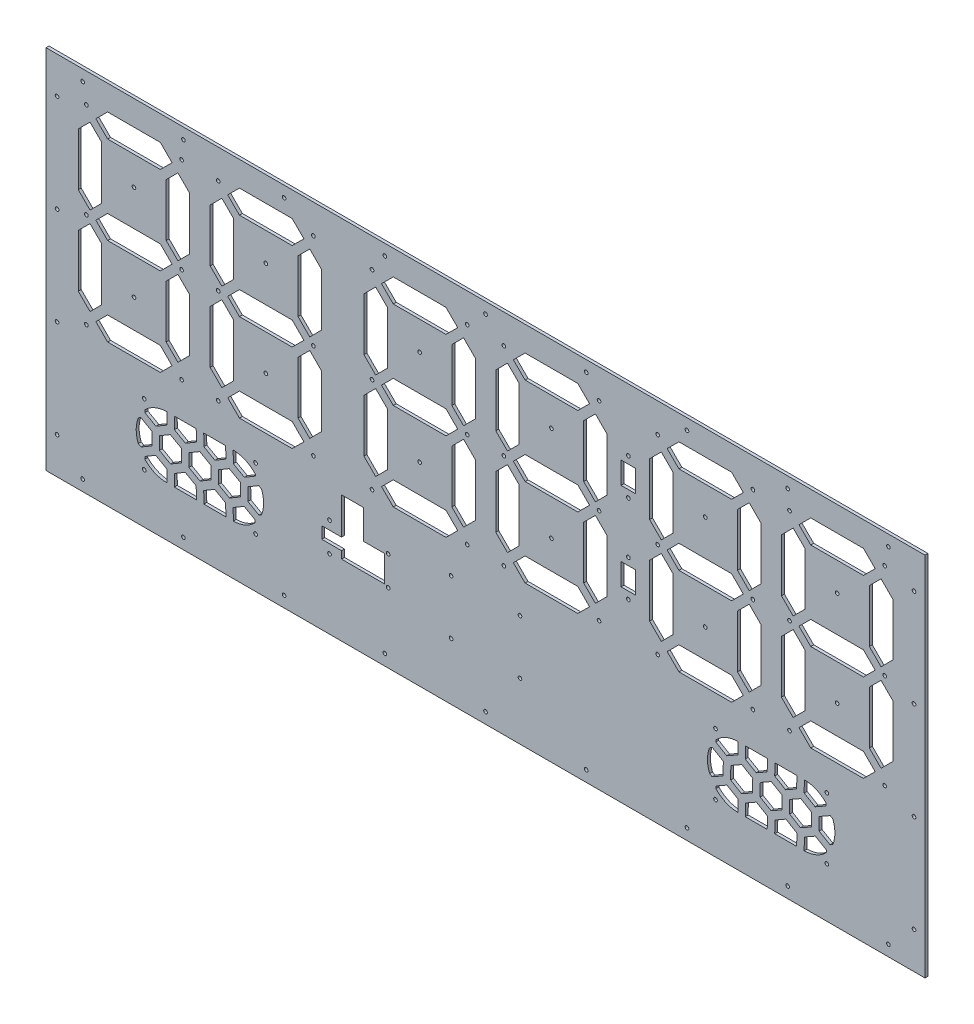
SolidWorks part; units mm, degrees
ref_plane "Alzado" through (0, 0, 0) normal (0, 0, 1) x (1, 0, 0)
ref_plane "Planta" through (0, 0, 0) normal (0, 1, 0) x (1, 0, 0)
ref_plane "Vista lateral" through (0, 0, 0) normal (1, 0, 0) x (0, 0, -1)
sketch "Croquis2" plane through (0, 0, 0) normal (0, 0, 1) x (1, 0, 0)
  line L1 (-300, -125) -> (300, -125)
  line L2 (-300, -125) -> (-300, 125)
  line L3 (-300, 125) -> (300, 125)
  line L4 (300, -125) -> (300, 125)
  line L5 (-300, -125) -> (300, 125) construction
  line L6 (-300, 125) -> (300, -125) construction
  point P0 (0, 0)
extrude "Saliente-Extruir1" add sketch "Croquis2" along normal blind 4
sketch "Croquis4" plane through (0, 0, 0) normal (0, 0, -1) x (-1, 0, 0)
  line L0 (0, 125) -> (0, 40) construction
  line L2 (-300, 125) -> (300, 125) construction
  line B0 (222, 92) -> (214, 100)
  line B1 (214, 100) -> (222, 108)
  line B2 (222, 108) -> (258, 108)
  line B3 (258, 108) -> (266, 100)
  line B4 (266, 100) -> (258, 92)
  line B5 (258, 92) -> (222, 92)
  line B6 (-262, -8) -> (-270, -16)
  line B7 (-270, -16) -> (-278, -8)
  line B8 (-278, -8) -> (-278, 28)
  line B9 (-278, 28) -> (-270, 36)
  line B10 (-270, 36) -> (-262, 28)
  line B11 (-262, 28) -> (-262, -8)
  line B12 (-222, 100) -> (-258, 100) construction
  line B13 (-258, 92) -> (-266, 100)
  line B14 (-266, 100) -> (-258, 108)
  line B15 (-258, 108) -> (-222, 108)
  line B16 (-222, 108) -> (-214, 100)
  line B17 (-214, 100) -> (-222, 92)
  line B18 (-222, 92) -> (-258, 92)
  line B19 (-168, -12) -> (-176, -20)
  line B20 (-176, -20) -> (-168, -28)
  line B21 (-168, -28) -> (-132, -28)
  line B22 (-132, -28) -> (-124, -20)
  line B23 (-124, -20) -> (-132, -12)
  line B24 (-132, -12) -> (-168, -12)
  line B25 (222, 32) -> (214, 40)
  line B26 (214, 40) -> (222, 48)
  line B27 (222, 48) -> (258, 48)
  line B28 (258, 48) -> (266, 40)
  line B29 (266, 40) -> (258, 32)
  line B30 (258, 32) -> (222, 32)
  line B31 (-168, 92) -> (-176, 100)
  line B32 (-176, 100) -> (-168, 108)
  line B33 (-168, 108) -> (-132, 108)
  line B34 (-132, 108) -> (-124, 100)
  line B35 (-124, 100) -> (-132, 92)
  line B36 (-132, 92) -> (-168, 92)
  line B37 (222, -12) -> (214, -20)
  line B38 (214, -20) -> (222, -28)
  line B39 (222, -28) -> (258, -28)
  line B40 (258, -28) -> (266, -20)
  line B41 (266, -20) -> (258, -12)
  line B42 (258, -12) -> (222, -12)
  line B43 (262, -8) -> (270, -16)
  line B44 (270, -16) -> (278, -8)
  line B45 (278, -8) -> (278, 28)
  line B46 (278, 28) -> (270, 36)
  line B47 (270, 36) -> (262, 28)
  line B48 (262, 28) -> (262, -8)
  line B49 (218, 88) -> (210, 96)
  line B50 (210, 96) -> (202, 88)
  line B51 (202, 88) -> (202, 52)
  line B52 (202, 52) -> (210, 44)
  line B53 (210, 44) -> (218, 52)
  line B54 (218, 52) -> (218, 88)
  line B55 (218, -8) -> (210, -16)
  line B56 (210, -16) -> (202, -8)
  line B57 (202, -8) -> (202, 28)
  line B58 (202, 28) -> (210, 36)
  line B59 (210, 36) -> (218, 28)
  line B60 (218, 28) -> (218, -8)
  line B61 (-128, -8) -> (-120, -16)
  line B62 (-120, -16) -> (-112, -8)
  line B63 (-112, -8) -> (-112, 28)
  line B64 (-112, 28) -> (-120, 36)
  line B65 (-120, 36) -> (-128, 28)
  line B66 (-128, 28) -> (-128, -8)
  line B67 (-168, 32) -> (-176, 40)
  line B68 (-176, 40) -> (-168, 48)
  line B69 (-168, 48) -> (-132, 48)
  line B70 (-132, 48) -> (-124, 40)
  line B71 (-124, 40) -> (-132, 32)
  line B72 (-132, 32) -> (-168, 32)
  line B73 (-262, 88) -> (-270, 96)
  line B74 (-270, 96) -> (-278, 88)
  line B75 (-278, 88) -> (-278, 52)
  line B76 (-278, 52) -> (-270, 44)
  line B77 (-270, 44) -> (-262, 52)
  line B78 (-262, 52) -> (-262, 88)
  line B79 (262, 88) -> (270, 96)
  line B80 (270, 96) -> (278, 88)
  line B81 (278, 88) -> (278, 52)
  line B82 (278, 52) -> (270, 44)
  line B83 (270, 44) -> (262, 52)
  line B84 (262, 52) -> (262, 88)
  line B85 (-218, 88) -> (-210, 96)
  line B86 (-210, 96) -> (-202, 88)
  line B87 (-202, 88) -> (-202, 52)
  line B88 (-202, 52) -> (-210, 44)
  line B89 (-210, 44) -> (-218, 52)
  line B90 (-218, 52) -> (-218, 88)
  line B91 (-258, 32) -> (-266, 40)
  line B92 (-266, 40) -> (-258, 48)
  line B93 (-258, 48) -> (-222, 48)
  line B94 (-222, 48) -> (-214, 40)
  line B95 (-214, 40) -> (-222, 32)
  line B96 (-222, 32) -> (-258, 32)
  line B97 (-218, -8) -> (-210, -16)
  line B98 (-210, -16) -> (-202, -8)
  line B99 (-202, -8) -> (-202, 28)
  line B100 (-202, 28) -> (-210, 36)
  line B101 (-210, 36) -> (-218, 28)
  line B102 (-218, 28) -> (-218, -8)
  line B103 (-258, -12) -> (-266, -20)
  line B104 (-266, -20) -> (-258, -28)
  line B105 (-258, -28) -> (-222, -28)
  line B106 (-222, -28) -> (-214, -20)
  line B107 (-214, -20) -> (-222, -12)
  line B108 (-222, -12) -> (-258, -12)
  line B109 (128, 88) -> (120, 96)
  line B110 (120, 96) -> (112, 88)
  line B111 (112, 88) -> (112, 52)
  line B112 (112, 52) -> (120, 44)
  line B113 (120, 44) -> (128, 52)
  line B114 (128, 52) -> (128, 88)
  line B115 (132, 92) -> (124, 100)
  line B116 (124, 100) -> (132, 108)
  line B117 (132, 108) -> (168, 108)
  line B118 (168, 108) -> (176, 100)
  line B119 (176, 100) -> (168, 92)
  line B120 (168, 92) -> (132, 92)
  line B121 (128, -8) -> (120, -16)
  line B122 (120, -16) -> (112, -8)
  line B123 (112, -8) -> (112, 28)
  line B124 (112, 28) -> (120, 36)
  line B125 (120, 36) -> (128, 28)
  line B126 (128, 28) -> (128, -8)
  line B127 (132, -12) -> (124, -20)
  line B128 (124, -20) -> (132, -28)
  line B129 (132, -28) -> (168, -28)
  line B130 (168, -28) -> (176, -20)
  line B131 (176, -20) -> (168, -12)
  line B132 (168, -12) -> (132, -12)
  line B133 (132, 32) -> (124, 40)
  line B134 (124, 40) -> (132, 48)
  line B135 (132, 48) -> (168, 48)
  line B136 (168, 48) -> (176, 40)
  line B137 (176, 40) -> (168, 32)
  line B138 (168, 32) -> (132, 32)
  line B139 (172, -8) -> (180, -16)
  line B140 (180, -16) -> (188, -8)
  line B141 (188, -8) -> (188, 28)
  line B142 (188, 28) -> (180, 36)
  line B143 (180, 36) -> (172, 28)
  line B144 (172, 28) -> (172, -8)
  line B145 (-128, 88) -> (-120, 96)
  line B146 (-120, 96) -> (-112, 88)
  line B147 (-112, 88) -> (-112, 52)
  line B148 (-112, 52) -> (-120, 44)
  line B149 (-120, 44) -> (-128, 52)
  line B150 (-128, 52) -> (-128, 88)
  line B151 (-180, 28) -> (-180, -8) construction
  line B152 (-172, -8) -> (-180, -16)
  line B153 (-180, -16) -> (-188, -8)
  line B154 (-188, -8) -> (-188, 28)
  line B155 (-188, 28) -> (-180, 36)
  line B156 (-180, 36) -> (-172, 28)
  line B157 (-172, 28) -> (-172, -8)
  line B158 (-172, 88) -> (-180, 96)
  line B159 (-180, 96) -> (-188, 88)
  line B160 (-188, 88) -> (-188, 52)
  line B161 (-188, 52) -> (-180, 44)
  line B162 (-180, 44) -> (-172, 52)
  line B163 (-172, 52) -> (-172, 88)
  line B164 (172, 88) -> (180, 96)
  line B165 (180, 96) -> (188, 88)
  line B166 (188, 88) -> (188, 52)
  line B167 (188, 52) -> (180, 44)
  line B168 (180, 44) -> (172, 52)
  line B169 (172, 52) -> (172, 88)
  line B170 (-2.5, 40) -> (2.5, 40) construction
  line B171 (87.5, 40) -> (107.5, 40) construction
  line B172 (-87.5, 40) -> (-107.5, 40) construction
  line B173 (-87.5, 40) -> (-2.5, 40) construction
  line B174 (-45, 110) -> (-45, -30) construction
  line B175 (-45, 40) -> (-15, 40) construction
  line B176 (-15, 40) -> (-15, 44) construction
  line B177 (-75, 96) -> (-71, 96) construction
  line B178 (-71, 96) -> (-71, 100) construction
  line B179 (2.5, 40) -> (87.5, 40) construction
  line B180 (45, 110) -> (45, -30) construction
  line B181 (45, 40) -> (75, 40) construction
  line B182 (75, 40) -> (75, 44) construction
  line B183 (15, 96) -> (19, 96) construction
  line B184 (19, 96) -> (19, 100) construction
  line B185 (192.5, 40) -> (197.5, 40) construction
  line B186 (-197.5, 40) -> (-192.5, 40) construction
  line B187 (-75, 44) -> (-75, 52) construction
  line B188 (-75, 52) -> (-75, 88) construction
  line B189 (-75, 88) -> (-75, 96) construction
  line B190 (-75, 52) -> (-83, 52) construction
  line B191 (-83, 52) -> (-67, 52) construction
  line B192 (-75, 88) -> (-83, 88) construction
  line B193 (-83, 88) -> (-67, 88) construction
  line B194 (-67, 88) -> (-75, 96)
  line B195 (-75, 96) -> (-83, 88)
  line B196 (-83, 88) -> (-83, 52)
  line B197 (-83, 52) -> (-75, 44)
  line B198 (-75, 44) -> (-67, 52)
  line B199 (-67, 52) -> (-67, 88)
  line B200 (-19, -20) -> (-27, -20) construction
  line B201 (-27, -20) -> (-63, -20) construction
  line B202 (-63, -20) -> (-71, -20) construction
  line B203 (-27, -20) -> (-27, -28) construction
  line B204 (-27, -28) -> (-27, -12) construction
  line B205 (-63, -20) -> (-63, -28) construction
  line B206 (-63, -28) -> (-63, -12) construction
  line B207 (-63, -12) -> (-71, -20)
  line B208 (-71, -20) -> (-63, -28)
  line B209 (-63, -28) -> (-27, -28)
  line B210 (-27, -28) -> (-19, -20)
  line B211 (-19, -20) -> (-27, -12)
  line B212 (-27, -12) -> (-63, -12)
  line B213 (-19, 40) -> (-27, 40) construction
  line B214 (-27, 40) -> (-63, 40) construction
  line B215 (-63, 40) -> (-71, 40) construction
  line B216 (-27, 40) -> (-27, 48) construction
  line B217 (-27, 48) -> (-27, 32) construction
  line B218 (-63, 40) -> (-63, 48) construction
  line B219 (-63, 48) -> (-63, 32) construction
  line B220 (-63, 32) -> (-71, 40)
  line B221 (-71, 40) -> (-63, 48)
  line B222 (-63, 48) -> (-27, 48)
  line B223 (-27, 48) -> (-19, 40)
  line B224 (-19, 40) -> (-27, 32)
  line B225 (-27, 32) -> (-63, 32)
  line B226 (-15, 36) -> (-15, 28) construction
  line B227 (-15, 28) -> (-15, -8) construction
  line B228 (-15, -8) -> (-15, -16) construction
  line B229 (-15, 28) -> (-7, 28) construction
  line B230 (-7, 28) -> (-23, 28) construction
  line B231 (-15, -8) -> (-7, -8) construction
  line B232 (-7, -8) -> (-23, -8) construction
  line B233 (-23, -8) -> (-15, -16)
  line B234 (-15, -16) -> (-7, -8)
  line B235 (-7, -8) -> (-7, 28)
  line B236 (-7, 28) -> (-15, 36)
  line B237 (-15, 36) -> (-23, 28)
  line B238 (-23, 28) -> (-23, -8)
  line B239 (15, 44) -> (15, 52) construction
  line B240 (15, 52) -> (15, 88) construction
  line B241 (15, 88) -> (15, 96) construction
  line B242 (15, 52) -> (7, 52) construction
  line B243 (7, 52) -> (23, 52) construction
  line B244 (15, 88) -> (7, 88) construction
  line B245 (7, 88) -> (23, 88) construction
  line B246 (23, 88) -> (15, 96)
  line B247 (15, 96) -> (7, 88)
  line B248 (7, 88) -> (7, 52)
  line B249 (7, 52) -> (15, 44)
  line B250 (15, 44) -> (23, 52)
  line B251 (23, 52) -> (23, 88)
  line B252 (-15, 44) -> (-15, 52) construction
  line B253 (-15, 52) -> (-15, 88) construction
  line B254 (-15, 88) -> (-15, 96) construction
  line B255 (-15, 52) -> (-7, 52) construction
  line B256 (-7, 52) -> (-23, 52) construction
  line B257 (-15, 88) -> (-7, 88) construction
  line B258 (-7, 88) -> (-23, 88) construction
  line B259 (-23, 88) -> (-15, 96)
  line B260 (-15, 96) -> (-7, 88)
  line B261 (-7, 88) -> (-7, 52)
  line B262 (-7, 52) -> (-15, 44)
  line B263 (-15, 44) -> (-23, 52)
  line B264 (-23, 52) -> (-23, 88)
  line B265 (-19, 100) -> (-27, 100) construction
  line B266 (-27, 100) -> (-63, 100) construction
  line B267 (-63, 100) -> (-71, 100) construction
  line B268 (-27, 100) -> (-27, 108) construction
  line B269 (-27, 108) -> (-27, 92) construction
  line B270 (-63, 100) -> (-63, 108) construction
  line B271 (-63, 108) -> (-63, 92) construction
  line B272 (-63, 92) -> (-71, 100)
  line B273 (-71, 100) -> (-63, 108)
  line B274 (-63, 108) -> (-27, 108)
  line B275 (-27, 108) -> (-19, 100)
  line B276 (-19, 100) -> (-27, 92)
  line B277 (-27, 92) -> (-63, 92)
  line B278 (75, 44) -> (75, 52) construction
  line B279 (75, 52) -> (75, 88) construction
  line B280 (75, 88) -> (75, 96) construction
  line B281 (75, 52) -> (83, 52) construction
  line B282 (83, 52) -> (67, 52) construction
  line B283 (75, 88) -> (83, 88) construction
  line B284 (83, 88) -> (67, 88) construction
  line B285 (67, 88) -> (75, 96)
  line B286 (75, 96) -> (83, 88)
  line B287 (83, 88) -> (83, 52)
  line B288 (83, 52) -> (75, 44)
  line B289 (75, 44) -> (67, 52)
  line B290 (67, 52) -> (67, 88)
  line B291 (15, 36) -> (15, 28) construction
  line B292 (15, 28) -> (15, -8) construction
  line B293 (15, -8) -> (15, -16) construction
  line B294 (15, 28) -> (7, 28) construction
  line B295 (7, 28) -> (23, 28) construction
  line B296 (15, -8) -> (7, -8) construction
  line B297 (7, -8) -> (23, -8) construction
  line B298 (23, -8) -> (15, -16)
  line B299 (15, -16) -> (7, -8)
  line B300 (7, -8) -> (7, 28)
  line B301 (7, 28) -> (15, 36)
  line B302 (15, 36) -> (23, 28)
  line B303 (23, 28) -> (23, -8)
  line B304 (-75, 36) -> (-75, 28) construction
  line B305 (-75, 28) -> (-75, -8) construction
  line B306 (-75, -8) -> (-75, -16) construction
  line B307 (-75, 28) -> (-83, 28) construction
  line B308 (-83, 28) -> (-67, 28) construction
  line B309 (-75, -8) -> (-83, -8) construction
  line B310 (-83, -8) -> (-67, -8) construction
  line B311 (-67, -8) -> (-75, -16)
  line B312 (-75, -16) -> (-83, -8)
  line B313 (-83, -8) -> (-83, 28)
  line B314 (-83, 28) -> (-75, 36)
  line B315 (-75, 36) -> (-67, 28)
  line B316 (-67, 28) -> (-67, -8)
  line B317 (71, 100) -> (63, 100) construction
  line B318 (63, 100) -> (27, 100) construction
  line B319 (27, 100) -> (19, 100) construction
  line B320 (63, 100) -> (63, 108) construction
  line B321 (63, 108) -> (63, 92) construction
  line B322 (27, 100) -> (27, 108) construction
  line B323 (27, 108) -> (27, 92) construction
  line B324 (27, 92) -> (19, 100)
  line B325 (19, 100) -> (27, 108)
  line B326 (27, 108) -> (63, 108)
  line B327 (63, 108) -> (71, 100)
  line B328 (71, 100) -> (63, 92)
  line B329 (63, 92) -> (27, 92)
  line B330 (107.5, 40) -> (192.5, 40) construction
  line B331 (150, 110) -> (150, -30) construction
  line B332 (150, 40) -> (180, 40) construction
  line B333 (180, 40) -> (180, 44) construction
  line B334 (120, 96) -> (124, 96) construction
  line B335 (124, 96) -> (124, 100) construction
  line B336 (-192.5, 40) -> (-107.5, 40) construction
  line B337 (-150, 110) -> (-150, -30) construction
  line B338 (-150, 40) -> (-120, 40) construction
  line B339 (-120, 40) -> (-120, 44) construction
  line B340 (-180, 96) -> (-176, 96) construction
  line B341 (-176, 96) -> (-176, 100) construction
  line B342 (197.5, 40) -> (282.5, 40) construction
  line B343 (240, 110) -> (240, -30) construction
  line B344 (240, 40) -> (270, 40) construction
  line B345 (270, 40) -> (270, 44) construction
  line B346 (210, 96) -> (214, 96) construction
  line B347 (214, 96) -> (214, 100) construction
  line B348 (-282.5, 40) -> (-197.5, 40) construction
  line B349 (-240, 110) -> (-240, -30) construction
  line B350 (-240, 40) -> (-210, 40) construction
  line B351 (-210, 40) -> (-210, 44) construction
  line B352 (-270, 96) -> (-266, 96) construction
  line B353 (-266, 96) -> (-266, 100) construction
  line B354 (71, 40) -> (63, 40) construction
  line B355 (63, 40) -> (27, 40) construction
  line B356 (27, 40) -> (19, 40) construction
  line B357 (63, 40) -> (63, 48) construction
  line B358 (63, 48) -> (63, 32) construction
  line B359 (27, 40) -> (27, 48) construction
  line B360 (27, 48) -> (27, 32) construction
  line B361 (27, 32) -> (19, 40)
  line B362 (19, 40) -> (27, 48)
  line B363 (27, 48) -> (63, 48)
  line B364 (63, 48) -> (71, 40)
  line B365 (71, 40) -> (63, 32)
  line B366 (63, 32) -> (27, 32)
  line B367 (75, 36) -> (75, 28) construction
  line B368 (75, 28) -> (75, -8) construction
  line B369 (75, -8) -> (75, -16) construction
  line B370 (75, 28) -> (83, 28) construction
  line B371 (83, 28) -> (67, 28) construction
  line B372 (75, -8) -> (83, -8) construction
  line B373 (83, -8) -> (67, -8) construction
  line B374 (67, -8) -> (75, -16)
  line B375 (75, -16) -> (83, -8)
  line B376 (83, -8) -> (83, 28)
  line B377 (83, 28) -> (75, 36)
  line B378 (75, 36) -> (67, 28)
  line B379 (67, 28) -> (67, -8)
  line B380 (71, -20) -> (63, -20) construction
  line B381 (63, -20) -> (27, -20) construction
  line B382 (27, -20) -> (19, -20) construction
  line B383 (63, -20) -> (63, -28) construction
  line B384 (63, -28) -> (63, -12) construction
  line B385 (27, -20) -> (27, -28) construction
  line B386 (27, -28) -> (27, -12) construction
  line B387 (27, -12) -> (19, -20)
  line B388 (19, -20) -> (27, -28)
  line B389 (27, -28) -> (63, -28)
  line B390 (63, -28) -> (71, -20)
  line B391 (71, -20) -> (63, -12)
  line B392 (63, -12) -> (27, -12)
  line B393 (-112, 88) -> (-83, 52) construction
  line B394 (-83, 88) -> (-112, 52) construction
  line B395 (-83, -8) -> (-112, 28) construction
  line B396 (-112, -8) -> (-83, 28) construction
  line B397 (-102.5, 17.5) -> (-92.5, 17.5)
  line B398 (-102.5, 77.5) -> (-92.5, 77.5)
  line B399 (-102.5, 77.5) -> (-102.5, 62.5)
  line B400 (-102.5, 62.5) -> (-92.5, 62.5)
  line B401 (-92.5, 77.5) -> (-92.5, 62.5)
  line B402 (-102.5, 77.5) -> (-92.5, 62.5) construction
  line B403 (-102.5, 62.5) -> (-92.5, 77.5) construction
  line B404 (-92.5, 2.5) -> (-92.5, 17.5)
  line B405 (-102.5, 2.5) -> (-92.5, 2.5)
  line B406 (-102.5, 2.5) -> (-102.5, 17.5)
  line B407 (-102.5, 17.5) -> (-92.5, 2.5) construction
  line B408 (-102.5, 2.5) -> (-92.5, 17.5) construction
  circle B409 centre (-77.5, -25) radius 1.25
  circle B410 centre (-12.5, -25) radius 1.25
  circle B411 centre (-12.5, 40) radius 1.25
  circle B412 centre (-45, 7.5) radius 1.25
  circle B413 centre (-77.5, 40) radius 1.25
  circle B414 centre (-45, 72.5) radius 1.25
  circle B415 centre (-77.5, 105) radius 1.25
  circle B416 centre (-12.5, 105) radius 1.25
  circle B417 centre (12.5, -25) radius 1.25
  circle B418 centre (77.5, -25) radius 1.25
  circle B419 centre (77.5, 40) radius 1.25
  circle B420 centre (45, 7.5) radius 1.25
  circle B421 centre (12.5, 40) radius 1.25
  circle B422 centre (45, 72.5) radius 1.25
  circle B423 centre (12.5, 105) radius 1.25
  circle B424 centre (77.5, 105) radius 1.25
  circle B425 centre (117.5, -25) radius 1.25
  circle B426 centre (182.5, -25) radius 1.25
  circle B427 centre (182.5, 40) radius 1.25
  circle B428 centre (150, 7.5) radius 1.25
  circle B429 centre (117.5, 40) radius 1.25
  circle B430 centre (150, 72.5) radius 1.25
  circle B431 centre (117.5, 105) radius 1.25
  circle B432 centre (182.5, 105) radius 1.25
  circle B433 centre (-182.5, -25) radius 1.25
  circle B434 centre (-117.5, -25) radius 1.25
  circle B435 centre (-117.5, 40) radius 1.25
  circle B436 centre (-150, 7.5) radius 1.25
  circle B437 centre (-182.5, 40) radius 1.25
  circle B438 centre (-150, 72.5) radius 1.25
  circle B439 centre (-182.5, 105) radius 1.25
  circle B440 centre (-117.5, 105) radius 1.25
  circle B441 centre (207.5, -25) radius 1.25
  circle B442 centre (272.5, -25) radius 1.25
  circle B443 centre (272.5, 40) radius 1.25
  circle B444 centre (240, 7.5) radius 1.25
  circle B445 centre (207.5, 40) radius 1.25
  circle B446 centre (240, 72.5) radius 1.25
  circle B447 centre (207.5, 105) radius 1.25
  circle B448 centre (272.5, 105) radius 1.25
  circle B449 centre (-272.5, -25) radius 1.25
  circle B450 centre (-207.5, -25) radius 1.25
  circle B451 centre (-207.5, 40) radius 1.25
  circle B452 centre (-240, 7.5) radius 1.25
  circle B453 centre (-272.5, 40) radius 1.25
  circle B454 centre (-240, 72.5) radius 1.25
  circle B455 centre (-272.5, 105) radius 1.25
  circle B456 centre (-207.5, 105) radius 1.25
sketch_block_instance "Bloque5-1"
sketch_block "Bloque5"
sketch_block_instance "Bloque1-40"
sketch_block "Bloque1"
sketch_block_instance "Bloque1-46"
sketch_block_instance "Bloque1-47"
sketch_block_instance "Bloque1-34"
sketch_block_instance "Bloque1-42"
sketch_block_instance "Bloque1-33"
sketch_block_instance "Bloque1-41"
sketch_block_instance "Bloque1-43"
sketch_block_instance "Bloque1-37"
sketch_block_instance "Bloque1-39"
sketch_block_instance "Bloque1-36"
sketch_block_instance "Bloque1-35"
sketch_block_instance "Bloque1-44"
sketch_block_instance "Bloque1-38"
sketch_block_instance "Bloque1-45"
sketch_block_instance "Bloque1-49"
sketch_block_instance "Bloque1-50"
sketch_block_instance "Bloque1-48"
sketch_block_instance "Bloque1-23"
sketch_block_instance "Bloque1-26"
sketch_block_instance "Bloque1-25"
sketch_block_instance "Bloque1-27"
sketch_block_instance "Bloque1-28"
sketch_block_instance "Bloque1-29"
sketch_block_instance "Bloque1-31"
sketch_block_instance "Bloque1-32"
sketch_block_instance "Bloque1-30"
sketch_block_instance "Bloque1-24"
extrude "Cortar-Extruir4" cut sketch "Croquis4" against normal blind 2
sketch "Croquis5" plane through (0, 0, 0) normal (0, 0, 1) x (1, 0, 0)
  line L0 (0, 125) -> (0, 40) construction
  line L178 (-282.5, 0) -> (-197.5, 0) construction
  line L223 (-300, 0) -> (-292.5, 0) construction
  line L224 (-300, 125) -> (-300, -125) construction
  line L225 (-292.5, -100) -> (-292.5, -33.3333) construction
  line L227 (-292.5, -33.3333) -> (-292.5, 33.3333) construction
  line L228 (-292.5, 117.5) -> (-292.5, 100) construction
  line L229 (-292.5, 33.3333) -> (-292.5, 100) construction
  line L230 (0, 125) -> (0, 112.4645) construction
  line L231 (292.5, 33.3333) -> (292.5, 100) construction
  line L232 (-292.5, 100) -> (-292.5, 117.5) construction
  line L233 (292.5, -33.3333) -> (292.5, 33.3333) construction
  line L234 (292.5, -100) -> (292.5, -33.3333) construction
  line L235 (300, 0) -> (292.5, 0) construction
  circle A52 centre (-292.5, 100) radius 1.25
  circle A58 centre (-292.5, -100) radius 1.25
  circle A59 centre (-292.5, 33.3333) radius 1.25
  circle A60 centre (-292.5, -33.3333) radius 1.25
  circle A61 centre (292.5, -33.3333) radius 1.25
  circle A62 centre (292.5, 33.3333) radius 1.25
  circle A63 centre (292.5, -100) radius 1.25
  circle A64 centre (292.5, 100) radius 1.25
  line B0 (-300, 125) -> (300, 125) construction
  line B1 (-292.5, 117.5) -> (292.5, 117.5) construction
  line B2 (-292.5, 117.5) -> (-275, 117.5) construction
  line B3 (-275, 117.5) -> (0, 117.5) construction
  line B4 (0, 117.5) -> (-137.5, 117.5) construction
  line B5 (-137.5, 117.5) -> (-275, 117.5) construction
  line B6 (-275, 117.5) -> (-206.25, 117.5) construction
  line B7 (-206.25, 117.5) -> (0, 117.5) construction
  line B8 (0, 117.5) -> (-137.5, 117.5) construction
  line B9 (-137.5, 117.5) -> (-68.75, 117.5) construction
  line B10 (137.5, 117.5) -> (68.75, 117.5) construction
  line B11 (275, 117.5) -> (206.25, 117.5) construction
  line B12 (137.5, 117.5) -> (275, 117.5) construction
  circle B13 centre (-275, 117.5) radius 1.25
  circle B14 centre (-206.25, 117.5) radius 1.25
  circle B15 centre (-137.5, 117.5) radius 1.25
  circle B16 centre (-68.75, 117.5) radius 1.25
  circle B17 centre (68.75, 117.5) radius 1.25
  circle B18 centre (137.5, 117.5) radius 1.25
  circle B19 centre (206.25, 117.5) radius 1.25
  circle B20 centre (275, 117.5) radius 1.25
  circle B21 centre (0, 117.5) radius 1.25
  line B22 (300, -125) -> (-300, -125) construction
  line B23 (292.5, -117.5) -> (-292.5, -117.5) construction
  line B24 (137.5, -117.5) -> (275, -117.5) construction
  line B25 (275, -117.5) -> (206.25, -117.5) construction
  line B26 (137.5, -117.5) -> (68.75, -117.5) construction
  line B27 (-137.5, -117.5) -> (-68.75, -117.5) construction
  line B28 (0, -117.5) -> (-137.5, -117.5) construction
  line B29 (-206.25, -117.5) -> (0, -117.5) construction
  line B30 (-275, -117.5) -> (-206.25, -117.5) construction
  line B31 (-137.5, -117.5) -> (-275, -117.5) construction
  line B32 (0, -117.5) -> (-137.5, -117.5) construction
  line B33 (-275, -117.5) -> (0, -117.5) construction
  circle B34 centre (0, -117.5) radius 1.25
  circle B35 centre (275, -117.5) radius 1.25
  circle B36 centre (206.25, -117.5) radius 1.25
  circle B37 centre (137.5, -117.5) radius 1.25
  circle B38 centre (68.75, -117.5) radius 1.25
  circle B39 centre (-68.75, -117.5) radius 1.25
  circle B40 centre (-137.5, -117.5) radius 1.25
  circle B41 centre (-206.25, -117.5) radius 1.25
  circle B42 centre (-275, -117.5) radius 1.25
  line B43 (-2.5, 40) -> (2.5, 40) construction
  line B44 (87.5, 40) -> (107.5, 40) construction
  line B45 (-87.5, 40) -> (-107.5, 40) construction
  line B46 (-87.5, 40) -> (-2.5, 40) construction
  line B47 (-45, 110) -> (-45, -30) construction
  line B48 (-45, 40) -> (-15, 40) construction
  line B49 (-15, 40) -> (-15, 44) construction
  line B50 (-75, 96) -> (-71, 96) construction
  line B51 (-71, 96) -> (-71, 100) construction
  line B52 (2.5, 40) -> (87.5, 40) construction
  line B53 (45, 110) -> (45, -30) construction
  line B54 (45, 40) -> (75, 40) construction
  line B55 (75, 40) -> (75, 44) construction
  line B56 (15, 96) -> (19, 96) construction
  line B57 (19, 96) -> (19, 100) construction
  line B58 (192.5, 40) -> (197.5, 40) construction
  line B59 (-197.5, 40) -> (-192.5, 40) construction
  line B60 (-75, 44) -> (-75, 52) construction
  line B61 (-75, 52) -> (-75, 88) construction
  line B62 (-75, 88) -> (-75, 96) construction
  line B63 (-75, 52) -> (-83, 52) construction
  line B64 (-83, 52) -> (-67, 52) construction
  line B65 (-75, 88) -> (-83, 88) construction
  line B66 (-83, 88) -> (-67, 88) construction
  line B67 (-19, -20) -> (-27, -20) construction
  line B68 (-27, -20) -> (-63, -20) construction
  line B69 (-63, -20) -> (-71, -20) construction
  line B70 (-27, -20) -> (-27, -28) construction
  line B71 (-27, -28) -> (-27, -12) construction
  line B72 (-63, -20) -> (-63, -28) construction
  line B73 (-63, -28) -> (-63, -12) construction
  line B74 (-19, 40) -> (-27, 40) construction
  line B75 (-27, 40) -> (-63, 40) construction
  line B76 (-63, 40) -> (-71, 40) construction
  line B77 (-27, 40) -> (-27, 48) construction
  line B78 (-27, 48) -> (-27, 32) construction
  line B79 (-63, 40) -> (-63, 48) construction
  line B80 (-63, 48) -> (-63, 32) construction
  line B81 (-15, 36) -> (-15, 28) construction
  line B82 (-15, 28) -> (-15, -8) construction
  line B83 (-15, -8) -> (-15, -16) construction
  line B84 (-15, 28) -> (-7, 28) construction
  line B85 (-7, 28) -> (-23, 28) construction
  line B86 (-15, -8) -> (-7, -8) construction
  line B87 (-7, -8) -> (-23, -8) construction
  line B88 (15, 44) -> (15, 52) construction
  line B89 (15, 52) -> (15, 88) construction
  line B90 (15, 88) -> (15, 96) construction
  line B91 (15, 52) -> (7, 52) construction
  line B92 (7, 52) -> (23, 52) construction
  line B93 (15, 88) -> (7, 88) construction
  line B94 (7, 88) -> (23, 88) construction
  line B95 (-15, 44) -> (-15, 52) construction
  line B96 (-15, 52) -> (-15, 88) construction
  line B97 (-15, 88) -> (-15, 96) construction
  line B98 (-15, 52) -> (-7, 52) construction
  line B99 (-7, 52) -> (-23, 52) construction
  line B100 (-15, 88) -> (-7, 88) construction
  line B101 (-7, 88) -> (-23, 88) construction
  line B102 (-19, 100) -> (-27, 100) construction
  line B103 (-27, 100) -> (-63, 100) construction
  line B104 (-63, 100) -> (-71, 100) construction
  line B105 (-27, 100) -> (-27, 108) construction
  line B106 (-27, 108) -> (-27, 92) construction
  line B107 (-63, 100) -> (-63, 108) construction
  line B108 (-63, 108) -> (-63, 92) construction
  line B109 (75, 44) -> (75, 52) construction
  line B110 (75, 52) -> (75, 88) construction
  line B111 (75, 88) -> (75, 96) construction
  line B112 (75, 52) -> (83, 52) construction
  line B113 (83, 52) -> (67, 52) construction
  line B114 (75, 88) -> (83, 88) construction
  line B115 (83, 88) -> (67, 88) construction
  line B116 (15, 36) -> (15, 28) construction
  line B117 (15, 28) -> (15, -8) construction
  line B118 (15, -8) -> (15, -16) construction
  line B119 (15, 28) -> (7, 28) construction
  line B120 (7, 28) -> (23, 28) construction
  line B121 (15, -8) -> (7, -8) construction
  line B122 (7, -8) -> (23, -8) construction
  line B123 (-75, 36) -> (-75, 28) construction
  line B124 (-75, 28) -> (-75, -8) construction
  line B125 (-75, -8) -> (-75, -16) construction
  line B126 (-75, 28) -> (-83, 28) construction
  line B127 (-83, 28) -> (-67, 28) construction
  line B128 (-75, -8) -> (-83, -8) construction
  line B129 (-83, -8) -> (-67, -8) construction
  line B130 (71, 100) -> (63, 100) construction
  line B131 (63, 100) -> (27, 100) construction
  line B132 (27, 100) -> (19, 100) construction
  line B133 (63, 100) -> (63, 108) construction
  line B134 (63, 108) -> (63, 92) construction
  line B135 (27, 100) -> (27, 108) construction
  line B136 (27, 108) -> (27, 92) construction
  line B137 (107.5, 40) -> (192.5, 40) construction
  line B138 (150, 110) -> (150, -30) construction
  line B139 (150, 40) -> (180, 40) construction
  line B140 (180, 40) -> (180, 44) construction
  line B141 (120, 96) -> (124, 96) construction
  line B142 (124, 96) -> (124, 100) construction
  line B143 (-192.5, 40) -> (-107.5, 40) construction
  line B144 (-150, 110) -> (-150, -30) construction
  line B145 (-150, 40) -> (-120, 40) construction
  line B146 (-120, 40) -> (-120, 44) construction
  line B147 (-180, 96) -> (-176, 96) construction
  line B148 (-176, 96) -> (-176, 100) construction
  line B149 (197.5, 40) -> (282.5, 40) construction
  line B150 (240, 110) -> (240, -30) construction
  line B151 (240, 40) -> (270, 40) construction
  line B152 (270, 40) -> (270, 44) construction
  line B153 (210, 96) -> (214, 96) construction
  line B154 (214, 96) -> (214, 100) construction
  line B155 (-240, 110) -> (-240, -30) construction
  line B156 (-240, 40) -> (-210, 40) construction
  line B157 (-210, 40) -> (-210, 44) construction
  line B158 (-270, 96) -> (-266, 96) construction
  line B159 (-266, 96) -> (-266, 100) construction
  line B160 (71, 40) -> (63, 40) construction
  line B161 (63, 40) -> (27, 40) construction
  line B162 (27, 40) -> (19, 40) construction
  line B163 (63, 40) -> (63, 48) construction
  line B164 (63, 48) -> (63, 32) construction
  line B165 (27, 40) -> (27, 48) construction
  line B166 (27, 48) -> (27, 32) construction
  line B167 (75, 36) -> (75, 28) construction
  line B168 (75, 28) -> (75, -8) construction
  line B169 (75, -8) -> (75, -16) construction
  line B170 (75, 28) -> (83, 28) construction
  line B171 (83, 28) -> (67, 28) construction
  line B172 (75, -8) -> (83, -8) construction
  line B173 (83, -8) -> (67, -8) construction
  line B174 (71, -20) -> (63, -20) construction
  line B175 (63, -20) -> (27, -20) construction
  line B176 (27, -20) -> (19, -20) construction
  line B177 (63, -20) -> (63, -28) construction
  line B178 (63, -28) -> (63, -12) construction
  line B179 (27, -20) -> (27, -28) construction
  line B180 (27, -28) -> (27, -12) construction
  line B181 (97.5, 117.5) -> (97.5, 42.5) construction
  line B182 (97.5, 42.5) -> (97.5, -2.5) construction
  line B183 (97.5, -2.5) -> (97.5, 22.5) construction
  line B184 (0, -37.5) -> (0, 117.5) construction
  line B185 (0, 40) -> (94.8332, 40) construction
  circle B186 centre (-77.5, -25) radius 1.25
  circle B187 centre (-12.5, -25) radius 1.25
  circle B188 centre (-12.5, 40) radius 1.25
  circle B189 centre (-45, 7.5) radius 1.25
  circle B190 centre (-77.5, 40) radius 1.25
  circle B191 centre (-45, 72.5) radius 1.25
  circle B192 centre (-77.5, 105) radius 1.25
  circle B193 centre (-12.5, 105) radius 1.25
  circle B194 centre (12.5, -25) radius 1.25
  circle B195 centre (77.5, -25) radius 1.25
  circle B196 centre (77.5, 40) radius 1.25
  circle B197 centre (45, 7.5) radius 1.25
  circle B198 centre (12.5, 40) radius 1.25
  circle B199 centre (45, 72.5) radius 1.25
  circle B200 centre (12.5, 105) radius 1.25
  circle B201 centre (77.5, 105) radius 1.25
  circle B202 centre (117.5, -25) radius 1.25
  circle B203 centre (182.5, -25) radius 1.25
  circle B204 centre (182.5, 40) radius 1.25
  circle B205 centre (150, 7.5) radius 1.25
  circle B206 centre (117.5, 40) radius 1.25
  circle B207 centre (150, 72.5) radius 1.25
  circle B208 centre (117.5, 105) radius 1.25
  circle B209 centre (182.5, 105) radius 1.25
  circle B210 centre (-182.5, -25) radius 1.25
  circle B211 centre (-117.5, -25) radius 1.25
  circle B212 centre (-117.5, 40) radius 1.25
  circle B213 centre (-150, 7.5) radius 1.25
  circle B214 centre (-182.5, 40) radius 1.25
  circle B215 centre (-150, 72.5) radius 1.25
  circle B216 centre (-182.5, 105) radius 1.25
  circle B217 centre (-117.5, 105) radius 1.25
  circle B218 centre (207.5, -25) radius 1.25
  circle B219 centre (272.5, -25) radius 1.25
  circle B220 centre (272.5, 40) radius 1.25
  circle B221 centre (240, 7.5) radius 1.25
  circle B222 centre (207.5, 40) radius 1.25
  circle B223 centre (240, 72.5) radius 1.25
  circle B224 centre (207.5, 105) radius 1.25
  circle B225 centre (272.5, 105) radius 1.25
  circle B226 centre (-272.5, -25) radius 1.25
  circle B227 centre (-207.5, -25) radius 1.25
  circle B228 centre (-207.5, 40) radius 1.25
  circle B229 centre (-240, 7.5) radius 1.25
  circle B230 centre (-272.5, 40) radius 1.25
  circle B231 centre (-240, 72.5) radius 1.25
  circle B232 centre (-272.5, 105) radius 1.25
  circle B233 centre (-207.5, 105) radius 1.25
  circle B234 centre (97.5, 22.5) radius 1.25
  circle B235 centre (97.5, -2.5) radius 1.25
  circle B236 centre (97.5, 57.5) radius 1.25
  circle B237 centre (97.5, 82.5) radius 1.25
sketch_block_instance "Bloque3-1"
sketch_block "Bloque3"
sketch_block_instance "Bloque4-1"
sketch_block "Bloque4"
sketch_block_instance "Bloque6-1"
sketch_block "Bloque6"
extrude "Cortar-Extruir3" cut sketch "Croquis5" along normal through all
sketch "Croquis8" plane through (0, 0, 4) normal (0, 0, 1) x (1, 0, 0)
  line L9 (-195, -45) -> (-150, -45) construction
  line L10 (-150, -45) -> (-150, -95) construction
  line L11 (-150, -95) -> (-240, -95) construction
  line L12 (-240, -95) -> (-240, -45) construction
  line L13 (-240, -45) -> (-195, -45) construction
  line L14 (-195, -45) -> (-195, -49) construction
  line L15 (-233, -49) -> (-157, -49) construction
  line L16 (-195, -95) -> (-195, -91) construction
  line L17 (-195, -91) -> (-157, -91) construction
  line L18 (-157, -91) -> (-233, -91) construction
  line L22 (-195, -49) -> (-195, -91) construction
  line L23 (-195, -91) -> (-195, -70) construction
  line L24 (-195, -70) -> (-172.5, -70) construction
  line L25 (-172.5, -70) -> (-217.5, -70) construction
  line L26 (-217.5, -70) -> (-217.5, -49) construction
  line L27 (-217.5, -70) -> (-217.5, -91) construction
  line L28 (-217.5, -91) -> (-172.5, -91) construction
  line L29 (-172.5, -91) -> (-172.5, -49) construction
  line L30 (-238.5, -70) -> (-238.5, -45) construction
  line L31 (-238.5, -45) -> (-238.5, -95) construction
  line L32 (-151.5, -70) -> (-151.5, -45) construction
  line L33 (-151.5, -45) -> (-151.5, -95) construction
  line L46 (172.5, -91) -> (172.5, -49) construction
  line L47 (217.5, -91) -> (172.5, -91) construction
  line L48 (217.5, -70) -> (217.5, -91) construction
  line L49 (217.5, -70) -> (217.5, -49) construction
  line L50 (172.5, -70) -> (217.5, -70) construction
  line L51 (195, -70) -> (172.5, -70) construction
  line L52 (195, -91) -> (195, -70) construction
  line L53 (195, -49) -> (195, -91) construction
  line L54 (157, -91) -> (233, -91) construction
  line L55 (195, -91) -> (157, -91) construction
  line L56 (195, -95) -> (195, -91) construction
  line L57 (233, -49) -> (157, -49) construction
  line L58 (195, -45) -> (195, -49) construction
  circle A0 centre (-233, -49) radius 1.25
  circle A1 centre (-233, -91) radius 1.25
  circle A2 centre (-157, -91) radius 1.25
  circle A3 centre (-157, -49) radius 1.25
  circle A4 centre (157, -49) radius 1.25
  circle A5 centre (157, -91) radius 1.25
  circle A12 centre (233, -91) radius 1.25
  circle A13 centre (233, -49) radius 1.25
  point P25 (-195, -49)
extrude "Cortar-Extruir6" cut sketch "Croquis8" against normal through all
sketch "Croquis11" plane through (0, 0, 0) normal (0, 0, -1) x (-1, 0, 0)
  circle A0 centre (-23.5, -49) radius 1.25
  circle A1 centre (23.5, -49) radius 1.25
  circle A2 centre (23.5, -86) radius 1.25
  circle A3 centre (-23.5, -86) radius 1.25
extrude "Cortar-Extruir9" cut sketch "Croquis11" against normal through all
sketch "Croquis9" plane through (0, 0, 4) normal (0, 0, 1) x (1, 0, 0)
  line L0 (-233, -49) -> (-157, -91) construction
  line L243 (-157, -91) -> (-157, -49) construction
  line L412 (-157, -49) -> (-233, -91) construction
  line L581 (0, 0) -> (0, -102.0978) construction
  line L740 (172.5, -91) -> (217.5, -49) construction
  line L741 (217.5, -91) -> (172.5, -49) construction
  line L742 (157, -49) -> (233, -91) construction
  line L743 (157, -91) -> (157, -49) construction
  line L744 (233, -49) -> (157, -91) construction
  line L745 (217.5406, -91.4879) -> (217.6206, -82.828)
  line L746 (225.0002, -95.8872) -> (217.5406, -91.4879)
  line L747 (232.5399, -91.6266) -> (225.0002, -95.8872)
  line L748 (232.62, -82.9667) -> (232.5399, -91.6266)
  line L749 (225.1603, -78.5674) -> (232.62, -82.9667)
  line L750 (217.6206, -82.828) -> (225.1603, -78.5674)
  line L751 (227.7003, -74.2606) -> (227.7803, -65.6007)
  line L752 (235.1599, -78.6599) -> (227.7003, -74.2606)
  line L753 (242.6996, -74.3993) -> (235.1599, -78.6599)
  line L754 (242.7797, -65.7394) -> (242.6996, -74.3993)
  line L767 (235.32, -61.3401) -> (242.7797, -65.7394)
  line L780 (-217.6206, -48.228) -> (-225.1603, -43.9674)
  line L793 (-225.1603, -43.9674) -> (-232.62, -48.3667)
  line L806 (-232.62, -48.3667) -> (-232.5399, -57.0266)
  line L819 (-232.5399, -57.0266) -> (-225.0002, -61.2872)
  line L832 (-225.0002, -61.2872) -> (-217.5406, -56.8879)
  line L845 (-217.5406, -56.8879) -> (-217.6206, -48.228)
  line L858 (-197.5006, -48.228) -> (-205.0404, -43.9674)
  line L871 (-205.0404, -43.9674) -> (-212.5, -48.3667)
  line L884 (-212.5, -48.3667) -> (-212.4199, -57.0266)
  line L897 (-212.4199, -57.0266) -> (-204.8802, -61.2872)
  line L910 (-204.8802, -61.2872) -> (-197.4206, -56.8879)
  line L923 (-197.4206, -56.8879) -> (-197.5006, -48.228)
  line L936 (-177.3807, -48.228) -> (-184.9204, -43.9674)
  line L949 (-184.9204, -43.9674) -> (-192.38, -48.3667)
  line L962 (-192.38, -48.3667) -> (-192.3, -57.0266)
  line L975 (-192.3, -57.0266) -> (-184.7603, -61.2872)
  line L988 (-184.7603, -61.2872) -> (-177.3006, -56.8879)
  line L1001 (-177.3006, -56.8879) -> (-177.3807, -48.228)
  line L1014 (-157.2607, -48.228) -> (-164.8004, -43.9674)
  line L1027 (-164.8004, -43.9674) -> (-172.2601, -48.3667)
  line L1040 (-172.2601, -48.3667) -> (-172.18, -57.0266)
  line L1053 (-172.18, -57.0266) -> (-164.6403, -61.2872)
  line L1066 (-164.6403, -61.2872) -> (-157.1806, -56.8879)
  line L1079 (-157.1806, -56.8879) -> (-157.2607, -48.228)
  line L1092 (-217.5, -49) -> (-172.5, -49)
  line L1105 (-217.5, -91) -> (-172.5, -91)
  line L1118 (-207.6603, -65.6007) -> (-215.2, -61.3401)
  line L1131 (-215.2, -61.3401) -> (-222.6597, -65.7394)
  line L1144 (-222.6597, -65.7394) -> (-222.5796, -74.3993)
  line L1157 (-222.5796, -74.3993) -> (-215.0399, -78.6599)
  line L1158 (227.7803, -65.6007) -> (235.32, -61.3401)
  line L1159 (147.2203, -74.2606) -> (147.3004, -65.6007)
  line L1160 (-215.0399, -78.6599) -> (-207.5803, -74.2606)
  line L1161 (154.68, -78.6599) -> (147.2203, -74.2606)
  line L1162 (162.2197, -74.3993) -> (154.68, -78.6599)
  line L1163 (162.2997, -65.7394) -> (162.2197, -74.3993)
  line L1164 (154.8401, -61.3401) -> (162.2997, -65.7394)
  line L1165 (147.3004, -65.6007) -> (154.8401, -61.3401)
  line L1166 (157.1806, -91.4879) -> (157.2607, -82.828)
  line L1173 (164.6403, -95.8872) -> (157.1806, -91.4879)
  line L1174 (172.18, -91.6266) -> (164.6403, -95.8872)
  line L1175 (172.2601, -82.9667) -> (172.18, -91.6266)
  line L1176 (164.8004, -78.5674) -> (172.2601, -82.9667)
  line L1177 (157.2607, -82.828) -> (164.8004, -78.5674)
  line L1178 (167.3403, -74.2606) -> (167.4204, -65.6007)
  line L1185 (174.8, -78.6599) -> (167.3403, -74.2606)
  line L1186 (182.3397, -74.3993) -> (174.8, -78.6599)
  line L1187 (182.4197, -65.7394) -> (182.3397, -74.3993)
  line L1188 (174.9601, -61.3401) -> (182.4197, -65.7394)
  line L1189 (167.4204, -65.6007) -> (174.9601, -61.3401)
  line L1190 (177.3006, -91.4879) -> (177.3807, -82.828)
  line L1197 (184.7603, -95.8872) -> (177.3006, -91.4879)
  line L1198 (192.3, -91.6266) -> (184.7603, -95.8872)
  line L1199 (192.38, -82.9667) -> (192.3, -91.6266)
  line L1200 (184.9204, -78.5674) -> (192.38, -82.9667)
  line L1201 (177.3807, -82.828) -> (184.9204, -78.5674)
  line L1202 (187.4603, -74.2606) -> (187.5404, -65.6007)
  line L1209 (194.9199, -78.6599) -> (187.4603, -74.2606)
  line L1210 (202.4596, -74.3993) -> (194.9199, -78.6599)
  line L1211 (202.5397, -65.7394) -> (202.4596, -74.3993)
  line L1212 (195.0801, -61.3401) -> (202.5397, -65.7394)
  line L1213 (187.5404, -65.6007) -> (195.0801, -61.3401)
  line L1214 (197.4206, -91.4879) -> (197.5006, -82.828)
  line L1221 (204.8802, -95.8872) -> (197.4206, -91.4879)
  line L1222 (212.4199, -91.6266) -> (204.8802, -95.8872)
  line L1223 (212.5, -82.9667) -> (212.4199, -91.6266)
  line L1224 (205.0404, -78.5674) -> (212.5, -82.9667)
  line L1225 (197.5006, -82.828) -> (205.0404, -78.5674)
  line L1226 (207.5803, -74.2606) -> (207.6603, -65.6007)
  line L1233 (215.0399, -78.6599) -> (207.5803, -74.2606)
  line L1234 (222.5796, -74.3993) -> (215.0399, -78.6599)
  line L1235 (222.6597, -65.7394) -> (222.5796, -74.3993)
  line L1236 (215.2, -61.3401) -> (222.6597, -65.7394)
  line L1237 (207.6603, -65.6007) -> (215.2, -61.3401)
  line L1238 (217.5, -91) -> (172.5, -91)
  line L1245 (217.5, -49) -> (172.5, -49)
  line L1246 (157.1806, -56.8879) -> (157.2607, -48.228)
  line L1247 (164.6403, -61.2872) -> (157.1806, -56.8879)
  line L1248 (172.18, -57.0266) -> (164.6403, -61.2872)
  line L1249 (172.2601, -48.3667) -> (172.18, -57.0266)
  line L1250 (164.8004, -43.9674) -> (172.2601, -48.3667)
  line L1257 (157.2607, -48.228) -> (164.8004, -43.9674)
  line L1258 (177.3006, -56.8879) -> (177.3807, -48.228)
  line L1259 (184.7603, -61.2872) -> (177.3006, -56.8879)
  line L1260 (192.3, -57.0266) -> (184.7603, -61.2872)
  line L1261 (192.38, -48.3667) -> (192.3, -57.0266)
  line L1262 (184.9204, -43.9674) -> (192.38, -48.3667)
  line L1269 (177.3807, -48.228) -> (184.9204, -43.9674)
  line L1270 (197.4206, -56.8879) -> (197.5006, -48.228)
  line L1271 (204.8802, -61.2872) -> (197.4206, -56.8879)
  line L1272 (212.4199, -57.0266) -> (204.8802, -61.2872)
  line L1273 (212.5, -48.3667) -> (212.4199, -57.0266)
  line L1274 (205.0404, -43.9674) -> (212.5, -48.3667)
  line L1281 (197.5006, -48.228) -> (205.0404, -43.9674)
  line L1282 (217.5406, -56.8879) -> (217.6206, -48.228)
  line L1283 (225.0002, -61.2872) -> (217.5406, -56.8879)
  line L1284 (232.5399, -57.0266) -> (225.0002, -61.2872)
  line L1285 (232.62, -48.3667) -> (232.5399, -57.0266)
  line L1286 (225.1603, -43.9674) -> (232.62, -48.3667)
  line L1293 (217.6206, -48.228) -> (225.1603, -43.9674)
  line L1511 (-207.5803, -74.2606) -> (-207.6603, -65.6007)
  line L1512 (-197.5006, -82.828) -> (-205.0404, -78.5674)
  line L1513 (-205.0404, -78.5674) -> (-212.5, -82.9667)
  line L1514 (-212.5, -82.9667) -> (-212.4199, -91.6266)
  line L1527 (-212.4199, -91.6266) -> (-204.8802, -95.8872)
  line L1528 (-204.8802, -95.8872) -> (-197.4206, -91.4879)
  line L1529 (-197.4206, -91.4879) -> (-197.5006, -82.828)
  line L1530 (-187.5404, -65.6007) -> (-195.0801, -61.3401)
  line L1531 (-195.0801, -61.3401) -> (-202.5397, -65.7394)
  line L1532 (-202.5397, -65.7394) -> (-202.4596, -74.3993)
  line L1533 (-202.4596, -74.3993) -> (-194.9199, -78.6599)
  line L1534 (-194.9199, -78.6599) -> (-187.4603, -74.2606)
  line L1535 (-187.4603, -74.2606) -> (-187.5404, -65.6007)
  line L1536 (-177.3807, -82.828) -> (-184.9204, -78.5674)
  line L1537 (-184.9204, -78.5674) -> (-192.38, -82.9667)
  line L1538 (-192.38, -82.9667) -> (-192.3, -91.6266)
  line L1539 (-192.3, -91.6266) -> (-184.7603, -95.8872)
  line L1540 (-184.7603, -95.8872) -> (-177.3006, -91.4879)
  line L1541 (-177.3006, -91.4879) -> (-177.3807, -82.828)
  line L1542 (-167.4204, -65.6007) -> (-174.9601, -61.3401)
  line L1543 (-174.9601, -61.3401) -> (-182.4197, -65.7394)
  line L1544 (-182.4197, -65.7394) -> (-182.3397, -74.3993)
  line L1545 (-182.3397, -74.3993) -> (-174.8, -78.6599)
  line L1546 (-174.8, -78.6599) -> (-167.3403, -74.2606)
  line L1547 (-167.3403, -74.2606) -> (-167.4204, -65.6007)
  line L1548 (-157.2607, -82.828) -> (-164.8004, -78.5674)
  line L1549 (-164.8004, -78.5674) -> (-172.2601, -82.9667)
  line L1550 (-172.2601, -82.9667) -> (-172.18, -91.6266)
  line L1551 (-172.18, -91.6266) -> (-164.6403, -95.8872)
  line L1552 (-164.6403, -95.8872) -> (-157.1806, -91.4879)
  line L1553 (-157.1806, -91.4879) -> (-157.2607, -82.828)
  line L1554 (-147.3004, -65.6007) -> (-154.8401, -61.3401)
  line L1555 (-154.8401, -61.3401) -> (-162.2997, -65.7394)
  line L1556 (-162.2997, -65.7394) -> (-162.2197, -74.3993)
  line L1557 (-162.2197, -74.3993) -> (-154.68, -78.6599)
  line L1558 (-154.68, -78.6599) -> (-147.2203, -74.2606)
  line L1559 (-147.2203, -74.2606) -> (-147.3004, -65.6007)
  line L1560 (-227.7803, -65.6007) -> (-235.32, -61.3401)
  line L1561 (-235.32, -61.3401) -> (-242.7797, -65.7394)
  line L1562 (-242.7797, -65.7394) -> (-242.6996, -74.3993)
  line L1563 (-242.6996, -74.3993) -> (-235.1599, -78.6599)
  line L1564 (-235.1599, -78.6599) -> (-227.7003, -74.2606)
  line L1565 (-227.7003, -74.2606) -> (-227.7803, -65.6007)
  line L1566 (-217.6206, -82.828) -> (-225.1603, -78.5674)
  line L1567 (-225.1603, -78.5674) -> (-232.62, -82.9667)
  line L1568 (-232.62, -82.9667) -> (-232.5399, -91.6266)
  line L1569 (-232.5399, -91.6266) -> (-225.0002, -95.8872)
  line L1570 (-225.0002, -95.8872) -> (-217.5406, -91.4879)
  line L1571 (-217.5406, -91.4879) -> (-217.6206, -82.828)
  line L1572 (-217.5, -91) -> (-172.5, -49) construction
  line L1573 (-172.5, -91) -> (-217.5, -49) construction
  circle A6 centre (-215.12, -70) radius 7.5 construction
  circle A7 centre (-195, -70) radius 7.5 construction
  circle A8 centre (-174.88, -70) radius 7.5 construction
  circle A9 centre (-154.76, -70) radius 7.5 construction
  circle A10 centre (-235.24, -70) radius 7.5 construction
  arc A11 (-217.5, -49) -> (-217.5, -91) centre (-217.5, -70) ccw
  arc A12 (-172.5, -91) -> (-172.5, -49) centre (-172.5, -70) ccw
  circle A13 centre (235.24, -70) radius 7.5 construction
  circle A14 centre (154.76, -70) radius 7.5 construction
  circle A15 centre (174.88, -70) radius 7.5 construction
  circle A16 centre (195, -70) radius 7.5 construction
  circle A17 centre (215.12, -70) radius 7.5 construction
  arc A18 (172.5, -91) -> (172.5, -49) centre (172.5, -70) cw
  arc A19 (217.5, -49) -> (217.5, -91) centre (217.5, -70) cw
extrude "Cortar-Extruir7" cut sketch "Croquis9" against normal through all contours L1237 L1226 L1233 L1234 L1235 L1236 | A19 L1282 L1283 L1284 L1285 | L1273 L1245 L1270 L1271 L1272 | L1261 L1245 L1258 L1259 L1260 | A18 L1246 L1247 L1248 L1249 | A18 L1161 L1162 L1163 L1164 L1165 | A18 L1175 L1176 L1177 L1166 | L1189 L1178 L1185 L1186 L1187 L1188 | L1238 L1199 L1200 L1201 L1190 | L1213 L1202 L1209 L1210 L1211 L1212 | L1238 L1223 L1224 L1225 L1214 | A19 L748 L749 L750 L745 | A19 L767 L1158 L751 L752 L753 | L1105 L1529 L1512 L1513 L1514 | L1105 L1541 L1536 L1537 L1538 | L1550 A12 L1553 L1548 L1549 | L1558 A12 L1554 L1555 L1556 L1557 | L1546 L1547 L1542 L1543 L1544 L1545 | L1534 L1535 L1530 L1531 L1532 L1533 | L1160 L1511 L1118 L1131 L1144 L1157 | L1568 A11 L1571 L1566 L1567 | L1561 A11 L1563 L1564 L1565 L1560 | L845 A11 L806 L819 L832 | L1092 L884 L897 L910 L923 | L1092 L962 L975 L988 L1001 | L1079 A12 L1040 L1053 L1066
sketch "Croquis12" plane through (0, 0, 0) normal (0, 0, -1) x (-1, 0, 0)
  line L0 (98.2931, -53.5) -> (98.2931, -68.5) construction
  line L1 (82.7, -75.5) -> (70, -75.5)
  line L2 (82.7, -75.5) -> (82.7, -59.5)
  line L3 (82.7, -59.5) -> (70, -59.5)
  line L4 (70, -75.5) -> (70, -59.5)
  line L5 (83.2931, -68.5) -> (98.2931, -68.5)
  line L6 (83.2931, -68.5) -> (83.2931, -53.5)
  line L7 (83.2931, -53.5) -> (98.2931, -53.5)
  line L8 (98.2931, -68.5) -> (98.2931, -53.5)
  line L9 (62.5, -53.5) -> (110.5, -53.5) construction
  line L11 (102.55, -64.5) -> (109.5, -64.5)
  line L12 (102.55, -64.5) -> (102.55, -70.5)
  line L13 (102.55, -70.5) -> (109.5, -70.5)
  line L14 (109.5, -64.5) -> (109.5, -70.5)
  circle A0 centre (66.5, -57.5) radius 1.25
  circle A1 centre (66.5, -77.5) radius 1.25
  circle A2 centre (106.5, -77.5) radius 1.25
  circle A3 centre (106.5, -57.5) radius 1.25
sketch "Croquis13" plane through (0, 0, 0) normal (0, 0, -1) x (-1, 0, 0)
  circle A0 centre (66.5, -57.5) radius 1.25
  circle A1 centre (66.5, -77.5) radius 1.25
  circle A2 centre (106.5, -77.5) radius 1.25
  circle A3 centre (106.5, -57.5) radius 1.25
extrude "Cortar-Extruir10" cut sketch "Croquis13" against normal through all
sketch "Croquis14" plane through (0, 0, 0) normal (0, 0, -1) x (-1, 0, 0)
  line L2 (68.85, -76.5) -> (68.85, -58.5)
  line L3 (68.85, -58.5) -> (83.2931, -58.5)
  line L8 (98.2931, -63.5) -> (98.2931, -53.5)
  line L10 (83.2931, -58.5) -> (83.2931, -53.5)
  line L12 (83.2931, -53.5) -> (83.2931, -38.5)
  line L13 (83.2931, -38.5) -> (98.2931, -38.5)
  line L14 (98.2931, -53.5) -> (98.2931, -38.5)
  line L17 (100.025, -63.5) -> (111.7931, -63.5)
  line L18 (111.7931, -63.5) -> (111.7931, -71.5)
  line L19 (100.025, -63.5) -> (98.2931, -63.5)
  line L21 (111.7931, -71.5) -> (98.2931, -71.5)
  line L22 (98.2931, -71.5) -> (98.2931, -76.5)
  line L23 (98.2931, -76.5) -> (68.85, -76.5)
  point P0 (76.35, -67.5)
  point P1 (106.025, -67.5)
extrude "Cortar-Extruir11" cut sketch "Croquis14" against normal blind 2
sketch "Croquis15" plane through (0, 0, 2) normal (0, 0, -1) x (-1, 0, 0)
  line L15 (75.7767, -62.094) -> (70.7767, -64.9807)
  line L16 (70.7767, -64.9807) -> (70.7767, -70.7542)
  line L17 (70.7767, -70.7542) -> (75.7767, -73.641)
  line L18 (75.7767, -73.641) -> (80.7767, -70.7542)
  line L19 (80.7767, -70.7542) -> (80.7767, -64.9807)
  line L20 (80.7767, -64.9807) -> (75.7767, -62.094)
  circle A0 centre (75.7767, -67.8675) radius 5 construction
extrude "Cortar-Extruir12" cut sketch "Croquis15" against normal through all
sketch "Croquis16" plane through (-300, 0, 0) normal (-1, 0, 0) x (0, 0, 1)
  line L1 (4, 125) -> (2, 125)
  line L2 (4, 125) -> (4, -125)
  line L3 (4, -125) -> (2, -125)
  line L4 (2, 125) -> (2, -125)
extrude "Cortar-Extruir13" cut sketch "Croquis16" against normal through all
